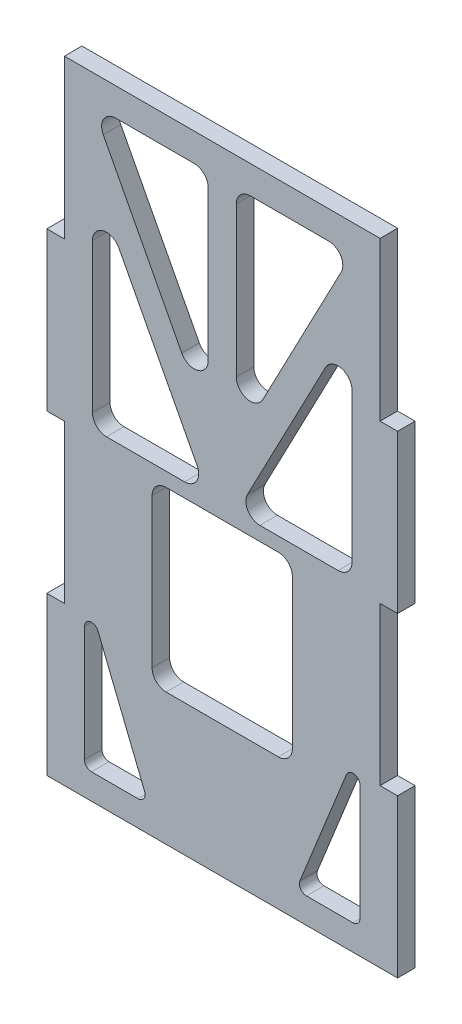
SolidWorks part; units mm, degrees
ref_plane "Front Plane" through (0, 0, 0) normal (0, 0, 1) x (1, 0, 0)
ref_plane "Top Plane" through (0, 0, 0) normal (0, 1, 0) x (1, 0, 0)
ref_plane "Right Plane" through (0, 0, 0) normal (1, 0, 0) x (0, 0, -1)
sketch "Sketch1" plane through (0, 0, 0) normal (0, 0, 1) x (1, 0, 0)
  line L74 (35.6207, 40.5798) -> (38.7957, 40.5798)
  line L80 (38.7957, 40.5798) -> (38.7957, 69.2404)
  line L81 (38.7957, 69.2404) -> (95.9457, 69.2404)
  line L82 (95.9457, 69.2404) -> (95.9457, 40.5798)
  line L83 (95.9457, 40.5798) -> (99.1207, 40.5798)
  line L84 (99.1207, 40.5798) -> (99.1207, 12.0048)
  line L85 (99.1207, 12.0048) -> (95.9457, 12.0048)
  line L86 (95.9457, 12.0048) -> (95.9457, -16.5702)
  line L87 (95.9457, -16.5702) -> (99.1207, -16.5702)
  line L88 (99.1207, -16.5702) -> (99.1207, -45.1452)
  line L89 (99.1207, -45.1452) -> (95.9457, -45.1452)
  line L105 (38.7957, -45.1452) -> (35.6207, -45.1452)
  line L106 (35.6207, -45.1452) -> (35.6207, -16.5702)
  line L107 (35.6207, -16.5702) -> (38.7957, -16.5702)
  line L108 (38.7957, -16.5702) -> (38.7957, 12.0048)
  line L109 (38.7957, 12.0048) -> (35.6207, 12.0048)
  line L110 (35.6207, 12.0048) -> (35.6207, 40.5798)
  line L111 (48.0797, 64.1604) -> (62.2907, 64.1604)
  line L112 (64.8307, 61.6204) -> (64.8307, 34.4902)
  line L113 (60.0407, 33.3116) -> (45.8297, 60.4418)
  line L114 (69.9107, 61.6204) -> (69.9107, 34.4902)
  line L115 (74.7007, 33.3116) -> (88.9117, 60.4418)
  line L116 (86.6617, 64.1604) -> (72.4507, 64.1604)
  line L117 (43.8757, 42.9008) -> (43.8757, 15.9004)
  line L118 (46.4157, 13.3604) -> (60.5587, 13.3604)
  line L119 (62.8087, 17.0789) -> (48.6657, 44.0794)
  line L120 (71.9326, 17.0789) -> (86.0757, 44.0794)
  line L121 (90.8657, 42.9008) -> (90.8657, 15.9004)
  line L122 (88.3257, 13.3604) -> (74.1826, 13.3604)
  line L153 (38.7957, 12.0048) -> (95.9457, 12.0048) construction
  line L154 (57.2107, 10.8204) -> (77.5307, 10.8204)
  line L155 (54.6707, 8.2804) -> (54.6707, -18.7252)
  line L156 (57.2107, -21.2652) -> (77.5307, -21.2652)
  line L157 (80.0707, 8.2804) -> (80.0707, -18.7252)
  line L158 (38.7957, -45.1452) -> (95.9457, -45.1452)
  line L159 (42.4323, -11.807) -> (42.4323, -40.5255)
  line L160 (42.4323, -40.5255) -> (54.0209, -40.5255)
  line L161 (54.0209, -40.5255) -> (42.4323, -11.807)
  line L162 (67.3707, -21.2652) -> (67.3707, -45.1452) construction
  line L163 (92.3091, -40.5255) -> (80.7205, -40.5255)
  line L164 (92.3091, -11.807) -> (92.3091, -40.5255)
  line L165 (80.7205, -40.5255) -> (92.3091, -11.807)
  arc A76 (43.8757, 15.9004) -> (46.4157, 13.3604) centre (46.4157, 15.9004) ccw
  arc A77 (43.8757, 42.9008) -> (48.6657, 44.0794) centre (46.4157, 42.9008) cw
  arc A78 (60.5587, 13.3604) -> (62.8087, 17.0789) centre (60.5587, 15.9004) ccw
  arc A79 (71.9326, 17.0789) -> (74.1826, 13.3604) centre (74.1826, 15.9004) ccw
  arc A80 (90.8657, 15.9004) -> (88.3257, 13.3604) centre (88.3257, 15.9004) cw
  arc A81 (86.0757, 44.0794) -> (90.8657, 42.9008) centre (88.3257, 42.9008) cw
  arc A82 (69.9107, 61.6204) -> (72.4507, 64.1604) centre (72.4507, 61.6204) cw
  arc A83 (86.6617, 64.1604) -> (88.9117, 60.4418) centre (86.6617, 61.6204) cw
  arc A84 (69.9107, 34.4902) -> (74.7007, 33.3116) centre (72.4507, 34.4902) ccw
  arc A85 (64.8307, 34.4902) -> (60.0407, 33.3116) centre (62.2907, 34.4902) cw
  arc A86 (62.2907, 64.1604) -> (64.8307, 61.6204) centre (62.2907, 61.6204) cw
  arc A87 (48.0797, 64.1604) -> (45.8297, 60.4418) centre (48.0797, 61.6204) ccw
  arc A88 (54.6707, -18.7252) -> (57.2107, -21.2652) centre (57.2107, -18.7252) ccw
  arc A89 (77.5307, -21.2652) -> (80.0707, -18.7252) centre (77.5307, -18.7252) ccw
  arc A90 (77.5307, 10.8204) -> (80.0707, 8.2804) centre (77.5307, 8.2804) cw
  arc A91 (57.2107, 10.8204) -> (54.6707, 8.2804) centre (57.2107, 8.2804) ccw
  point P21 (42.4323, -11.807)
  point P146 (90.8657, 8.1948)
  point P147 (69.9107, 8.1948)
  point P148 (43.8757, 8.1948)
  dimension "D19" = 2.54
  dimension "D25" = 2.54
  dimension "D1" = 5.08
  dimension "D2" = 5.08
  dimension "D3" = 5.08
  dimension "D4" = 5.08
  dimension "D7" = 5.08
  dimension "D8" = 5.08
  dimension "D12" = 29.21
  dimension "D13" = 63.5
  dimension "D17" = 15.875
  dimension "D18" = 58.42
  dimension "D20" = 50.8
extrude "Boss-Extrude1" add sketch "Sketch1" along normal blind 3.175
fillet "Fillet1" radius 1.27 6 edges at (80.7205, -40.5255, 1.5875) (92.3091, -11.807, 1.5875) (92.3091, -40.5255, 1.5875) (54.0209, -40.5255, 1.5875) (42.4323, -11.807, 1.5875) (42.4323, -40.5255, 1.5875)
